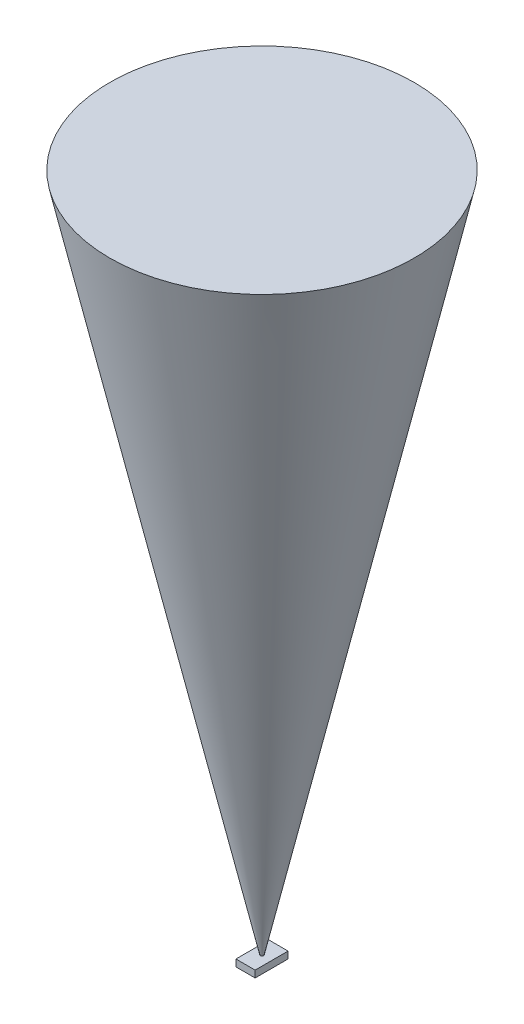
SolidWorks part; units mm, degrees
ref_plane "Plan de face" through (0, 0, 0) normal (0, 0, 1) x (1, 0, 0)
ref_plane "Plan de dessus" through (0, 0, 0) normal (0, 1, 0) x (1, 0, 0)
ref_plane "Plan de droite" through (0, 0, 0) normal (1, 0, 0) x (0, 0, -1)
sketch "Esquisse1" plane through (0, 0, 0) normal (0, 1, 0) x (1, 0, 0)
  line L0 (-1.4, 2.4) -> (1.4, -2.4) construction
  line L1 (-1.4, 2.4) -> (1.4, 2.4)
  line L2 (-1.4, 2.4) -> (-1.4, -2.4)
  line L3 (-1.4, -2.4) -> (1.4, -2.4)
  line L4 (1.4, 2.4) -> (1.4, -2.4)
  line L5 (1.4, -2.4) -> (1.4661, -2.4661) construction
  dimension "D1" = 2.8
  dimension "D2" = 4.8
extrude "Boss.-Extru.1" add sketch "Esquisse1" along normal blind 1
sketch "Esquisse2" plane through (0, 0, 0) normal (1, 0, 0) x (0, 0, -1)
  line L0 (0, 0) -> (0, 114.8594) construction
  line L1 (0, 0) -> (0, 100)
  line L2 (0, 100) -> (22.1695, 100)
  line L3 (22.1695, 100) -> (0, 0)
  dimension "D1" = 100
  dimension "D2" = 12.5
revolve "Révolution1" add sketch "Esquisse2" angle 360 about L0
